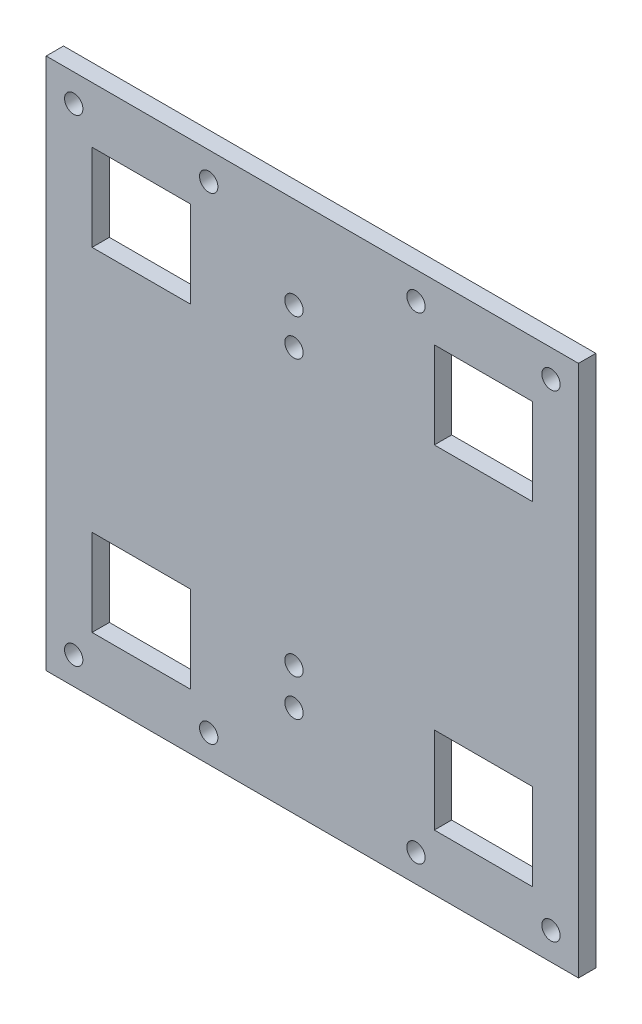
SolidWorks part; units mm, degrees
ref_plane "Front Plane" through (0, 0, 0) normal (0, 0, 1) x (1, 0, 0)
ref_plane "Top Plane" through (0, 0, 0) normal (0, 1, 0) x (1, 0, 0)
ref_plane "Right Plane" through (0, 0, 0) normal (1, 0, 0) x (0, 0, -1)
sketch "Sketch1" plane through (0, 0, 0) normal (0, 0, 1) x (1, 0, 0)
  line L0 (32.8752, 184.15) -> (32.8752, 0) construction
  line L1 (0, 0) -> (184.15, 0)
  line L2 (0, 0) -> (0, 184.15)
  line L3 (0, 184.15) -> (184.15, 184.15)
  line L4 (184.15, 0) -> (184.15, 184.15)
  line L5 (15.8752, 164.7622) -> (49.8752, 164.7622)
  line L6 (15.8752, 164.7622) -> (15.8752, 134.7622)
  line L7 (15.8752, 134.7622) -> (49.8752, 134.7622)
  line L8 (49.8752, 164.7622) -> (49.8752, 134.7622)
  line L9 (15.8752, 49.3878) -> (49.8752, 49.3878)
  line L10 (15.8752, 49.3878) -> (15.8752, 19.3878)
  line L11 (15.8752, 19.3878) -> (49.8752, 19.3878)
  line L12 (49.8752, 49.3878) -> (49.8752, 19.3878)
  line L13 (134.2748, 164.7622) -> (168.2748, 164.7622)
  line L14 (134.2748, 164.7622) -> (134.2748, 134.7622)
  line L15 (134.2748, 134.7622) -> (168.2748, 134.7622)
  line L16 (168.2748, 164.7622) -> (168.2748, 134.7622)
  line L17 (134.2748, 49.3878) -> (168.2748, 49.3878)
  line L18 (134.2748, 49.3878) -> (134.2748, 19.3878)
  line L19 (134.2748, 19.3878) -> (168.2748, 19.3878)
  line L20 (168.2748, 49.3878) -> (168.2748, 19.3878)
  line L21 (32.8752, 0) -> (151.2748, 0) construction
  line L22 (151.2748, 0) -> (151.2748, 184.15) construction
  line L23 (92.075, 184.15) -> (92.075, 0) construction
  line L25 (85.725, 152.4) -> (85.725, 139.7) construction
  circle A0 centre (9.525, 174.625) radius 3.175
  circle A1 centre (56.2254, 174.625) radius 3.175
  circle A2 centre (127.9246, 174.625) radius 3.175
  circle A3 centre (174.625, 174.625) radius 3.175
  circle A5 centre (85.725, 152.4) radius 3.175
  circle A7 centre (85.725, 139.7) radius 3.175
  circle A9 centre (9.525, 9.525) radius 3.175
  circle A10 centre (85.725, 44.45) radius 3.175
  circle A11 centre (56.2254, 9.525) radius 3.175
  circle A13 centre (85.725, 31.75) radius 3.175
  circle A14 centre (127.9246, 9.525) radius 3.175
  circle A15 centre (174.6174, 9.525) radius 3.175
  dimension "D3" = 6.35
  dimension "D20" = 12.7
  dimension "D26" = 6.35
  dimension "D1" = 184.15
  dimension "D2" = 184.15
  dimension "D4" = 34
  dimension "D5" = 30
  dimension "D6" = 46.7004
  dimension "D7" = 46.7004
  dimension "D8" = 46.6928
  dimension "D9" = 46.7004
  dimension "D10" = 9.525
  dimension "D11" = 9.525
  dimension "D12" = 9.525
  dimension "D13" = 9.525
  dimension "D14" = 32.8752
  dimension "D15" = 32.8752
  dimension "D16" = 17
  dimension "D17" = 17
  dimension "D18" = 19.3878
  dimension "D19" = 19.3878
  dimension "D21" = 6.35
  dimension "D22" = 12.7
  dimension "D23" = 31.75
  dimension "D25" = 31.75
extrude "Boss-Extrude1" add sketch "Sketch1" along normal blind 5.9944
